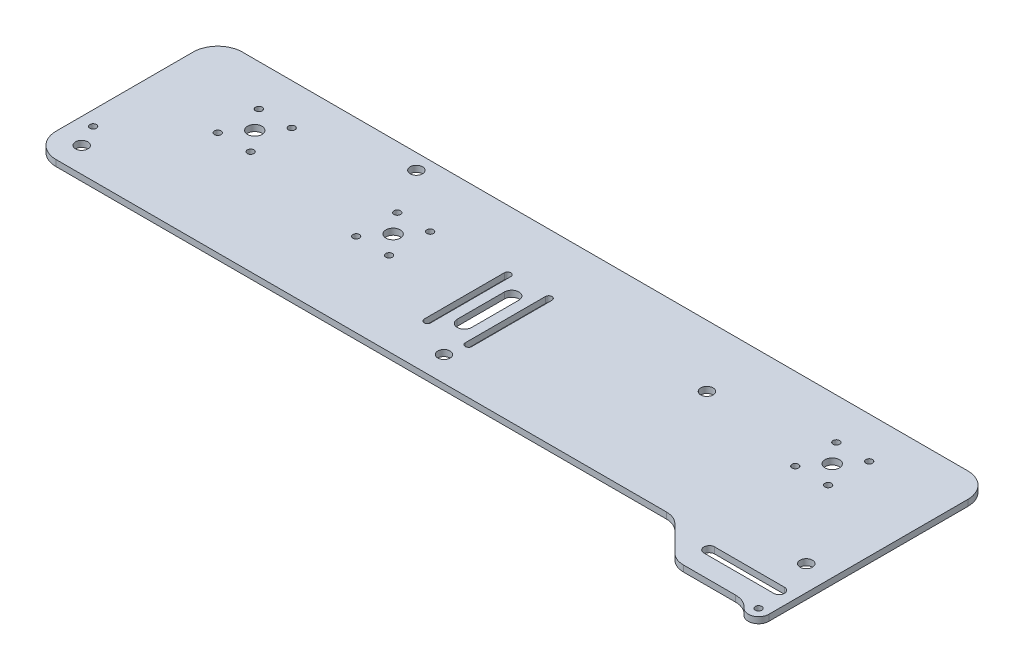
SolidWorks part; units mm, degrees
material "ACM"
ref_plane "Plano frontal" through (0, 0, 0) normal (0, 0, 1) x (1, 0, 0)
ref_plane "Plano superior" through (0, 0, 0) normal (0, 1, 0) x (1, 0, 0)
ref_plane "Plano direito" through (0, 0, 0) normal (1, 0, 0) x (0, 0, -1)
sketch "Esboço1" plane through (0, 0, 0) normal (0, 1, 0) x (1, 0, 0)
  line L2 (140.965, 10) -> (-62.7345, 0) construction
  line L4 (132.965, 0) -> (148.965, 0) construction
  line L6 (188.965, -38.6487) -> (188.965, 28)
  line L7 (176.965, 40) -> (-176.0908, 40)
  line L8 (-188.0908, 28) -> (-188.0908, -38.6487)
  line L9 (132.965, 0) -> (132.965, 20) construction
  line L11 (132.965, 20) -> (148.965, 20) construction
  line L12 (148.965, 0) -> (148.965, 20) construction
  line L13 (132.965, 0) -> (148.965, 20) construction
  line L14 (132.965, 20) -> (148.965, 0) construction
  line L15 (-148.0908, 0) -> (-132.0908, 0) construction
  line L16 (-148.0908, 0) -> (-148.0908, 20) construction
  line L17 (-148.0908, 20) -> (-132.0908, 20) construction
  line L18 (-132.0908, 0) -> (-132.0908, 20) construction
  line L19 (-176.0908, -50.6487) -> (176.965, -50.6487)
  line L20 (-148.0908, 0) -> (-132.0908, 20) construction
  line L21 (-148.0908, 20) -> (-132.0908, 0) construction
  line L22 (-70.7345, -10) -> (-54.7345, -10) construction
  line L23 (-70.7345, -10) -> (-70.7345, 10) construction
  line L24 (-70.7345, 10) -> (-54.7345, 10) construction
  line L25 (-54.7345, -10) -> (-54.7345, 10) construction
  line L26 (-70.7345, -10) -> (-54.7345, 10) construction
  line L27 (-70.7345, 10) -> (-54.7345, -10) construction
  arc A0 (176.965, -50.6487) -> (188.965, -38.6487) centre (176.965, -38.6487) ccw
  arc A1 (188.965, 28) -> (176.965, 40) centre (176.965, 28) ccw
  arc A2 (-188.0908, 28) -> (-176.0908, 40) centre (-176.0908, 28) cw
  arc A3 (-188.0908, -38.6487) -> (-176.0908, -50.6487) centre (-176.0908, -38.6487) ccw
  circle A7 centre (-62.7345, 0) radius 3.5
  circle A8 centre (176.7481, -38.4318) radius 3
  circle A9 centre (0.4371, -38.4318) radius 3
  circle A10 centre (79.965, 10) radius 3
  circle A11 centre (-140.0908, 10) radius 3.5
  circle A13 centre (-148.0908, 0) radius 1.6
  circle A14 centre (-132.0908, 0) radius 1.6
  circle A15 centre (-132.0908, 20) radius 1.6
  circle A16 centre (-148.0908, 20) radius 1.6
  circle A17 centre (-70.7345, -10) radius 1.6
  circle A18 centre (-70.7345, 10) radius 1.6
  circle A19 centre (-54.7345, 10) radius 1.6
  circle A20 centre (-54.7345, -10) radius 1.6
  circle A21 centre (-62.7345, 0) radius 25 construction
  circle A22 centre (-83.9303, 32.5) radius 7.5 construction
  circle A23 centre (-140.0908, 10) radius 48 construction
  circle A24 centre (-83.9303, 32.5) radius 3
  circle A25 centre (-175.8739, -38.4318) radius 3
  circle A26 centre (140.965, 10) radius 3.5
  circle A27 centre (148.965, 0) radius 1.6
  circle A28 centre (148.965, 20) radius 1.6
  circle A29 centre (132.965, 0) radius 1.6
  circle A30 centre (132.965, 20) radius 1.6
  circle A33 centre (-181.0908, -27.6487) radius 1.6
  circle A34 centre (181.965, -27.6487) radius 1.6 construction
  point P33 (0.4371, 40)
  dimension "D2" = 377.0558
  dimension "D4" = 7
  dimension "D6" = 12.2169
  dimension "D8" = 203.9448
  dimension "D10" = 48
  dimension "D12" = 16
  dimension "D15" = 20
  dimension "D17" = 6
  dimension "D1" = 12
  dimension "D7" = 40
  dimension "D9" = 30
  dimension "D11" = 7
  dimension "D16" = 3.2
  dimension "D20" = 3.2
  dimension "D25" = 56.1605
  dimension "D26" = 61
  dimension "D27" = 50
  dimension "D28" = 15
  dimension "D29" = 96
  dimension "D3" = 90.6487
  dimension "D5" = 12.2169
  dimension "D13" = 16
  dimension "D14" = 20
  dimension "D18" = 12.2169
  dimension "D19" = 30
  dimension "D21" = 16
  dimension "D22" = 20
  dimension "D23" = 48
  dimension "D24" = 7.5
  dimension "D30" = 7
  dimension "D31" = 7
  dimension "D32" = 23
extrude "Ressalto-extrusão1" add sketch "Esboço1" against normal blind 3
sketch "Esboço2" plane through (0, -3, 0) normal (0, -1, 0) x (1, 0, 0)
  line L0 (147.365, 56.2487) -> (181.365, 56.2487) construction
  line L5 (143.2229, 38.6487) -> (188.965, 38.6487)
  line L6 (143.2229, 38.6487) -> (143.2229, 68.8487)
  line L9 (143.2229, 68.8487) -> (188.965, 68.8487)
  line L10 (188.965, 38.6487) -> (188.965, 68.8487)
  line L11 (147.365, 58.8487) -> (181.365, 58.8487)
  line L12 (147.365, 53.6487) -> (181.365, 53.6487)
  line L13 (143.2229, 68.8487) -> (113.0229, 38.6487)
  line L14 (113.0229, 38.6487) -> (143.2229, 38.6487)
  line L16 (-176.0908, 50.6487) -> (176.965, 50.6487) construction
  circle A0 centre (183.965, 68.8487) radius 1.6
  circle A4 centre (-175.8739, 38.4318) radius 7.5 construction
  arc A5 (147.365, 58.8487) -> (147.365, 53.6487) centre (147.365, 56.2487) ccw
  arc A6 (181.365, 53.6487) -> (181.365, 58.8487) centre (181.365, 56.2487) ccw
  circle A8 centre (183.965, 68.8487) radius 5
  point P7 (164.365, 56.2487)
  point P12 (183.965, 56.2487)
  point P15 (144.765, 56.2487)
  dimension "D1" = 34
  dimension "D4" = 10
  dimension "D6" = 15
  dimension "D7" = 2.6
  dimension "D9" = 3.2
  dimension "D2" = 5
  dimension "D3" = 45
  dimension "D5" = 10
  dimension "D8" = 3
extrude "Ressalto-extrusão2" add sketch "Esboço2" against normal up to surface (3 mm away)
fillet "Filete2" radius 10 3 edges at (125.0229, -1.5, 50.6487) (143.2229, -1.5, 68.8487) (178.965, -1.5, 68.8487)
sketch "Esboço3" plane through (0, 0, 0) normal (0, 1, 0) x (1, 0, 0)
  line L0 (140.965, 10) -> (-62.7345, 0) construction
  line L1 (-7.7345, 2.7001) -> (-7.7345, -20.2999) construction
  line L2 (-4.2345, 2.7001) -> (-4.2345, -20.2999)
  line L3 (-11.2345, 2.7001) -> (-11.2345, -20.2999)
  line L4 (2.2655, 10.7001) -> (2.2655, -12.2999) construction
  line L5 (3.8655, 10.7001) -> (3.8655, -12.2999)
  line L6 (0.6655, 10.7001) -> (0.6655, -12.2999)
  line L7 (2.2655, -5.2999) -> (2.2655, -28.2999) construction
  line L8 (3.8655, -5.2999) -> (3.8655, -28.2999)
  line L9 (0.6655, -5.2999) -> (0.6655, -28.2999)
  line L10 (-7.7345, -20.2999) -> (-7.7345, -31.3543) construction
  line L11 (-17.7345, 10.7001) -> (-17.7345, -12.2999) construction
  line L12 (-19.3345, 10.7001) -> (-19.3345, -12.2999)
  line L13 (-16.1345, 10.7001) -> (-16.1345, -12.2999)
  line L14 (-17.7345, -5.2999) -> (-17.7345, -28.2999) construction
  line L15 (-19.3345, -5.2999) -> (-19.3345, -28.2999)
  line L16 (-16.1345, -5.2999) -> (-16.1345, -28.2999)
  line L17 (7.0083, -5.2999) -> (7.0083, 10.7001) construction
  arc A0 (-4.2345, 2.7001) -> (-11.2345, 2.7001) centre (-7.7345, 2.7001) ccw
  arc A1 (-11.2345, -20.2999) -> (-4.2345, -20.2999) centre (-7.7345, -20.2999) ccw
  arc A2 (3.8655, 10.7001) -> (0.6655, 10.7001) centre (2.2655, 10.7001) ccw
  arc A3 (0.6655, -12.2999) -> (3.8655, -12.2999) centre (2.2655, -12.2999) ccw
  arc A4 (3.8655, -5.2999) -> (0.6655, -5.2999) centre (2.2655, -5.2999) ccw
  arc A5 (0.6655, -28.2999) -> (3.8655, -28.2999) centre (2.2655, -28.2999) ccw
  arc A6 (-19.3345, 10.7001) -> (-16.1345, 10.7001) centre (-17.7345, 10.7001) cw
  arc A7 (-16.1345, -12.2999) -> (-19.3345, -12.2999) centre (-17.7345, -12.2999) cw
  arc A8 (-19.3345, -5.2999) -> (-16.1345, -5.2999) centre (-17.7345, -5.2999) cw
  arc A9 (-16.1345, -28.2999) -> (-19.3345, -28.2999) centre (-17.7345, -28.2999) cw
  circle A10 centre (-54.7345, 10) radius 1.6 construction
  circle A11 centre (-62.7345, 0) radius 3.5 construction
  point P6 (-7.7345, -8.7999)
  point P11 (2.2655, -0.7999)
  point P18 (2.2655, -16.7999)
  point P29 (-17.7345, -0.7999)
  point P36 (-17.7345, -16.7999)
  point P49 (7.0083, 2.7001)
  dimension "D1" = 16
  dimension "D2" = 23
  dimension "D3" = 20
  dimension "D4" = 55
extrude "Corte-extrusão1" cut sketch "Esboço3" against normal through all contours L8 A5 L9 A4 | L5 A3 L6 A2 | A0 L3 A1 L2 | L13 A7 L12 A6 | L15 A9 L16 A8
